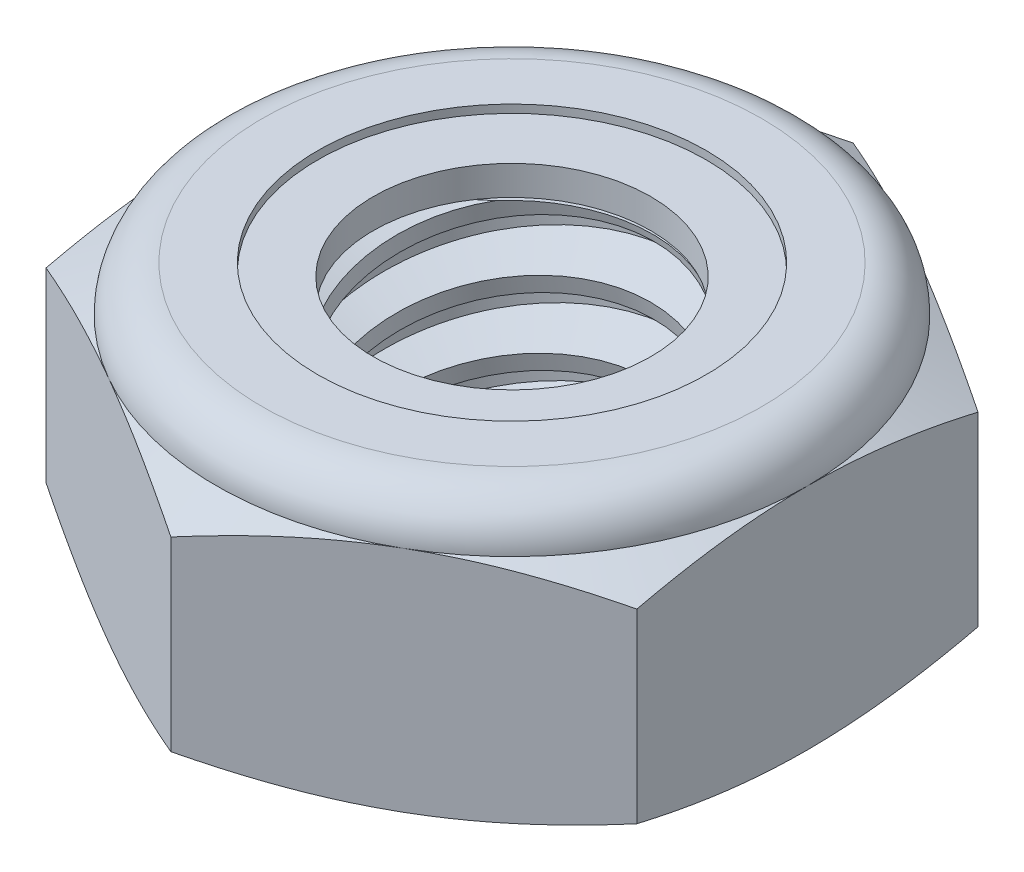
SolidWorks part; units mm, degrees
ref_plane "Front" through (0, 0, 0) normal (0, 0, 1) x (1, 0, 0)
ref_plane "Top" through (0, 0, 0) normal (0, 1, 0) x (1, 0, 0)
ref_plane "Right" through (0, 0, 0) normal (1, 0, 0) x (0, 0, -1)
sketch "Sketch1" plane through (0, 0, 0) normal (0, 1, 0) x (1, 0, 0)
  line L1 (0, 6.4158) -> (-5.5563, 3.2079)
  line L2 (-5.5563, 3.2079) -> (-5.5563, -3.2079)
  line L3 (-5.5563, -3.2079) -> (0, -6.4158)
  line L4 (0, -6.4158) -> (5.5562, -3.2079)
  line L5 (5.5562, -3.2079) -> (5.5562, 3.2079)
  line L6 (5.5562, 3.2079) -> (0, 6.4158)
  circle A0 centre (0, 0) radius 5.5563 construction
  dimension "Hex Flats" = 11.1125
extrude "Extrude1" add sketch "Sketch1" along normal blind 5.1594
sketch "Sketch2" plane through (0, 0, 0) normal (1, 0, 0) x (0, 0, -1)
  line L0 (-3.175, 0) -> (-3.175, 5.1594) construction
  line L1 (0, 0) -> (3.175, 0)
  line L2 (0, 0) -> (0, 5.1594)
  line L3 (0, 5.1594) -> (3.175, 5.1594)
  line L4 (3.175, 0) -> (3.175, 5.1594)
  line L5 (-3.2079, 5.1594) -> (3.2079, 5.1594) construction
  line L7 (0, -3.175) -> (0, 0) construction
  dimension "Thread Dia" = 6.35
revolve "Revolve1" add sketch "Sketch2" angle 360 about L7
sketch "Sketch3" plane through (0, 0, 0) normal (1, 0, 0) x (0, 0, -1)
  line L0 (3.175, 5.1594) -> (-3.175, 5.1594) construction
  line L1 (-3.175, 5.1594) -> (-3.175, 3.8894) construction
  line L2 (-3.175, 3.8894) -> (3.175, 5.1594) construction
  line L3 (3.175, 5.1594) -> (3.2061, 5.0037) construction
  line L4 (3.2061, 5.0037) -> (3.4241, 3.914)
  line L5 (3.4241, 3.914) -> (2.6722, 4.1684)
  line L6 (2.6722, 4.1684) -> (2.6099, 4.4797)
  line L7 (2.6099, 4.4797) -> (3.2061, 5.0037)
  line L8 (2.641, 4.3241) -> (3.3151, 4.4589) construction
  line L9 (3.175, 5.1594) -> (3.175, 4.4309) construction
  line L10 (3.175, 4.4309) -> (-3.175, 3.1609) construction
  line L11 (-3.175, 3.1609) -> (-3.175, 3.8894) construction
  line L12 (-0.2727, 5.1594) -> (0.2727, 2.4323) construction
  line L13 (-3.175, 0) -> (-3.175, 5.1594) construction
  line L14 (0, 5.1594) -> (3.175, 5.1594) construction
  line L15 (3.175, 0) -> (3.175, 5.1594) construction
  point P13 (0, 3.7959)
  dimension "D1" = 0.1588
  dimension "D2" = 0.3175
  dimension "Thread Pitch" = 1.27
  dimension "D4" = 60
  dimension "D5" = 1.27
revolve "Cut-Revolve1" cut sketch "Sketch3" angle 360 about L12
pattern_linear "LPattern1" count 4 spacing 1.27 along (0, -1, 0) count 2 spacing 1.27 along (0, 1, 0) of "Cut-Revolve1"
sketch "Sketch4" plane through (0, 0, 0) normal (1, 0, 0) x (0, 0, -1)
  line L0 (0, 5.1594) -> (3.175, 5.1594)
  line L1 (3.175, 5.1594) -> (2.6099, 4.8959)
  line L2 (2.6099, 4.8959) -> (2.6099, 0.2635)
  line L3 (2.6099, 0.2635) -> (3.175, 0)
  line L4 (3.175, 0) -> (0, 0)
  line L5 (0, 0) -> (0, 5.1594)
  line L6 (3.175, 0) -> (3.175, 5.1594) construction
  line L7 (0, 5.1594) -> (3.175, 5.1594) construction
  line L8 (0, 0) -> (3.175, 0) construction
  line L9 (0, 0) -> (0, 5.1594) construction
  line L10 (0, 5.1594) -> (0, 5.7829) construction
  dimension "D1" = 25
revolve "Cut-Revolve2" cut sketch "Sketch4" angle 360 about L10
combine bodies "Combine1" operation type subtract main body 112 bodies to subtract 111
sketch "Sketch5" plane through (0, 0, 0) normal (1, 0, 0) x (0, 0, -1)
  line L0 (0, 0) -> (5.5563, 0)
  line L1 (5.5563, 0) -> (6.4158, 0.4008)
  line L2 (6.4158, 0.4008) -> (6.4158, 3.8987)
  line L3 (6.4158, 3.8987) -> (5.5562, 4.2995)
  line L4 (4.6964, 5.1594) -> (4.6964, 6.4294)
  line L5 (4.6964, 6.4294) -> (7.6858, 6.4294)
  line L6 (7.6858, 6.4294) -> (7.6858, -1.27)
  line L7 (7.6858, -1.27) -> (0, -1.27)
  line L8 (0, -1.27) -> (0, 0)
  line L9 (5.5562, 4.2995) -> (5.5563, 0) construction
  line L10 (0, 0) -> (3.175, 0) construction
  line L13 (6.4158, 2.1497) -> (7.6858, 2.1497) construction
  line L14 (6.4158, 5.1594) -> (6.4158, 0) construction
  line L15 (0, 0) -> (0, 6.4294) construction
  line L20 (0, 6.4294) -> (4.6964, 6.4294) construction
  line L22 (0, 5.1594) -> (3.175, 5.1594) construction
  arc A0 (5.5562, 4.2995) -> (4.6964, 5.1594) centre (4.6964, 4.2995) ccw
  dimension "D1" = 25
  dimension "D2" = 1.27
  dimension "D3" = 5.1594
  dimension "D4" = 0.8599
revolve "Cut-Revolve3" cut sketch "Sketch5" angle 360 about L15
sketch "Sketch6" plane through (0, 0, 0) normal (1, 0, 0) x (0, 0, -1)
  line L0 (0, 4.2995) -> (5.4039, 4.2995)
  line L1 (4.6964, 5.007) -> (3.6531, 5.007)
  line L2 (0, 6.4294) -> (0, 4.2995)
  line L3 (3.6531, 6.4294) -> (0, 6.4294)
  line L4 (0, 6.4294) -> (4.6964, 6.4294) construction
  line L5 (0, 0) -> (0, 6.4294) construction
  line L6 (0, 6.4294) -> (0, 44.323) construction
  line L7 (3.6531, 5.007) -> (3.6531, 6.4294)
  line L8 (4.6964, 5.1594) -> (4.6964, 5.007) construction
  line L9 (3.6531, 5.007) -> (2.6099, 5.007) construction
  line L10 (2.6099, 5.007) -> (2.6099, 4.8959) construction
  arc A0 (5.4039, 4.2995) -> (4.6964, 5.007) centre (4.6964, 4.2995) ccw
  arc A1 (5.5562, 4.2995) -> (4.6964, 5.1594) centre (4.6964, 4.2995) ccw construction
  dimension "D1" = 0.1524
revolve "Cut-Revolve4" cut sketch "Sketch6" angle 360 about L6
sketch "Sketch7" plane through (0, 0, 0) normal (1, 0, 0) x (0, 0, -1)
  line L0 (2.6099, 4.3757) -> (5.323, 4.3757)
  line L1 (4.6964, 4.9308) -> (2.6099, 4.9308)
  line L2 (2.6099, 4.9308) -> (2.6099, 4.3757)
  line L3 (2.6099, 4.3757) -> (0, 4.3757) construction
  line L4 (0, 4.3757) -> (0, 4.9308) construction
  line L5 (0, 4.9308) -> (2.6099, 4.9308) construction
  line L6 (2.6099, 4.3757) -> (2.6099, 4.2995) construction
  line L7 (0, 4.2995) -> (5.4039, 4.2995) construction
  line L8 (4.6964, 4.9308) -> (4.6964, 5.007) construction
  arc A0 (5.323, 4.3757) -> (4.6964, 4.9308) centre (4.6964, 4.2995) ccw
  arc A2 (5.4039, 4.2995) -> (4.6964, 5.007) centre (4.6964, 4.2995) ccw construction
  dimension "D1" = 0.0762
revolve "Revolve2" add sketch "Sketch7" angle 360 about L4
equation "\"D1@Sketch3\"=\"Thread Pitch@Sketch3\"/8"
equation "\"D2@Sketch3\"=\"Thread Pitch@Sketch3\"/4"
equation "\"D5@Sketch3\"=\"Thread Pitch@Sketch3\""
equation "\"D4@LPattern1\"=\"Thread Pitch@Sketch3\""
equation "\"D3@LPattern1\"=\"Thread Pitch@Sketch3\""
equation "\"D1@LPattern1\"=\"Height@Extrude1\"/\"Thread Pitch@Sketch3\""
equation "\"D4@Sketch5\"=\"Height@Extrude1\"/6"
